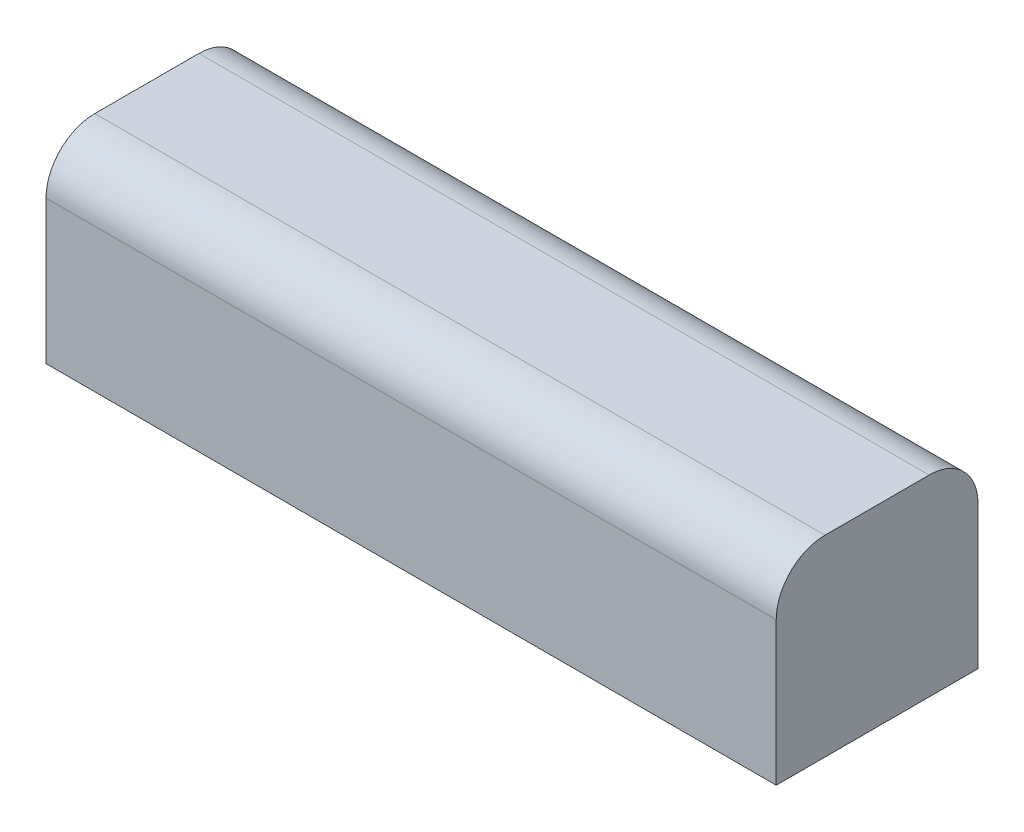
SolidWorks part; units mm, degrees
ref_plane "Front Plane" through (0, 0, 0) normal (0, 0, 1) x (1, 0, 0)
ref_plane "Top Plane" through (0, 0, 0) normal (0, 1, 0) x (1, 0, 0)
ref_plane "Right Plane" through (0, 0, 0) normal (1, 0, 0) x (0, 0, -1)
sketch "Sketch1" plane through (0, 0, 0) normal (0, 1, 0) x (1, 0, 0)
  line L1 (-38, -10.5) -> (38, -10.5)
  line L2 (-38, -10.5) -> (-38, 10.5)
  line L3 (-38, 10.5) -> (38, 10.5)
  line L4 (38, -10.5) -> (38, 10.5)
  line L5 (-38, -10.5) -> (38, 10.5) construction
  line L6 (-38, 10.5) -> (38, -10.5) construction
  point P0 (0, 0)
  dimension "D1" = 76
  dimension "D2" = 21
extrude "Boss-Extrude1" add sketch "Sketch1" along normal blind 20
fillet "Fillet1" radius 5.08 2 edges at (0, 20, -10.5) (0, 20, 10.5)
sketch "Sketch2" plane through (0, 0, 0) normal (0, -1, 0) x (1, 0, 0)
  line L1 (-38, -10.5) -> (38, -10.5) construction
  line L2 (-38, -10.5) -> (-38, 10.5) construction
  line L3 (-38, 10.5) -> (38, 10.5) construction
  line L4 (38, -10.5) -> (38, 10.5) construction
  line L5 (-38, -10.5) -> (38, 10.5) construction
  line L6 (-38, 10.5) -> (38, -10.5) construction
  circle A0 centre (0, 0) radius 1.5
  point P0 (0, 0)
  dimension "D1" = 3
extrude "Cut-Extrude1" cut sketch "Sketch2" against normal blind 2.54
